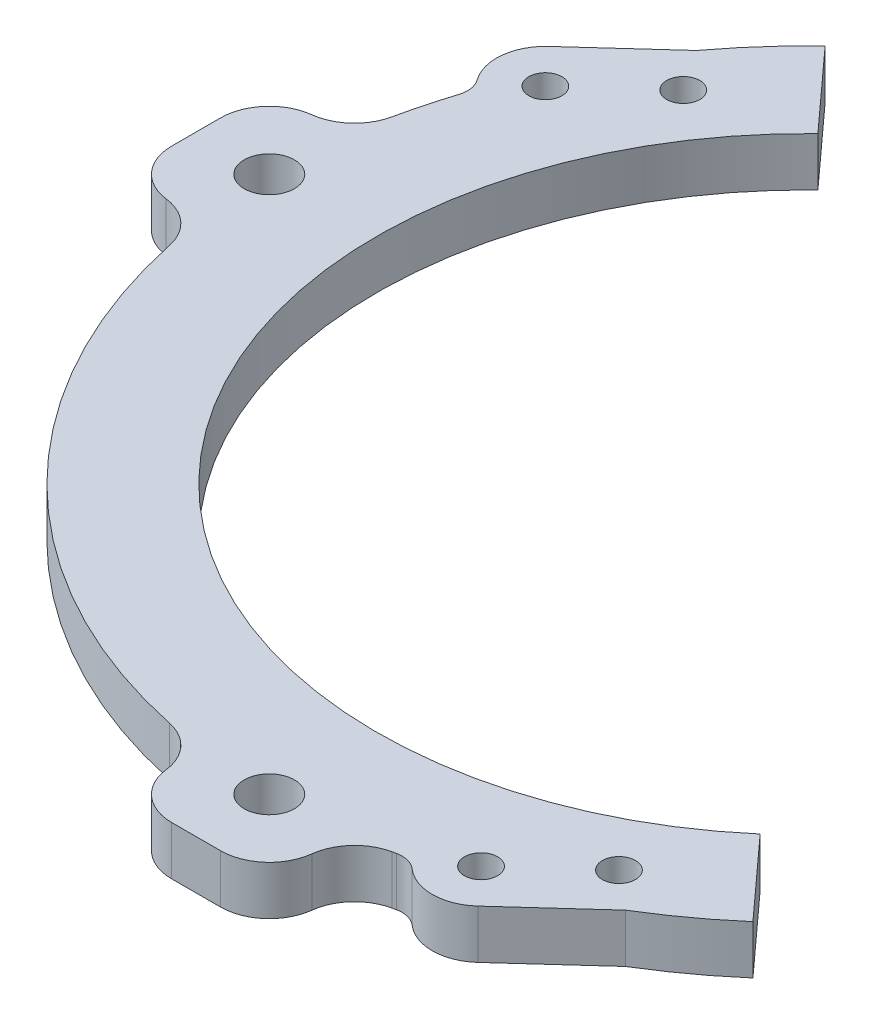
SolidWorks part; units mm, degrees
material "6061-T6 (SS)"
ref_plane "Front Plane" through (0, 0, 0) normal (0, 0, 1) x (1, 0, 0)
ref_plane "Top Plane" through (0, 0, 0) normal (0, 1, 0) x (1, 0, 0)
ref_plane "Right Plane" through (0, 0, 0) normal (1, 0, 0) x (0, 0, -1)
sketch "Sketch1" plane through (0, 0, 0) normal (0, 1, 0) x (1, 0, 0)
  circle A0 centre (0, 0) radius 55.88
  circle A1 centre (0, 0) radius 69.85
  dimension "D1" = 111.76
  dimension "D2" = 139.7
extrude "Boss-Extrude1" add sketch "Sketch1" along normal blind 6.35
sketch "Sketch5" plane through (0, 6.35, 0) normal (0, 1, 0) x (1, 0, 0)
  line L0 (0, 0) -> (0, 63.5) construction
  line L1 (-9.525, 63.5) -> (9.525, 63.5)
  line L2 (-9.525, 63.5) -> (-9.525, 73.025)
  line L3 (-3.175, 79.375) -> (3.175, 79.375)
  line L4 (9.525, 63.5) -> (9.525, 73.025)
  arc A0 (-9.525, 73.025) -> (-3.175, 79.375) centre (-3.175, 73.025) cw
  arc A1 (3.175, 79.375) -> (9.525, 73.025) centre (3.175, 73.025) cw
  point P10 (-9.525, 79.375)
  point P13 (9.525, 79.375)
  dimension "D4" = 6.35
  dimension "D1" = 63.5
  dimension "D2" = 79.375
  dimension "D3" = 19.05
extrude "Boss-Extrude2" add sketch "Sketch5" against normal blind 6.35
fillet "Fillet1" radius 6.35 2 edges at (9.525, 3.175, -69.1975) (-9.525, 3.175, -69.1975)
pattern_circular "CirPattern2" count 4 over 360 about axis through (0, 0, 0) along (0, 1, 0) of "Boss-Extrude2", "Fillet1"
hole_wizard "F (0.257) Diameter Hole1" positions "Sketch2" profile "Sketch3" hole size "F" standard "ANSI Inch" end condition through all
sketch "Sketch2" plane through (0, 6.35, 0) normal (0, 1, 0) x (1, 0, 0)
  point P0 (69.85, 0)
  dimension "D1" = 69.85
sketch "Sketch3" plane through (69.85, 6.35, 0) normal (1, 0, 0) x (0, 0, 1)
  line L0 (0, 0) -> (0, 6.35)
  line L1 (0, 6.35) -> (3.2639, 6.35)
  line L2 (3.2639, 6.35) -> (3.2639, 0)
  line L5 (3.2639, 0) -> (0, 0)
  line L11 (0, -6.35) -> (0, 107.95) construction
  dimension "Thru Hole Dia." = 6.5278
  dimension "Thru Hole Depth" = 6.35
pattern_circular "CirPattern1" count 4 over 360 about axis through (0, 0, 0) along (0, 1, 0) of "F (0.257) Diameter Hole1"
sketch "Sketch6" plane through (0, 0, 0) normal (0, -1, 0) x (1, 0, 0)
  line L0 (-57.4966, -60.8844) -> (55.1474, 63.0202)
  line L1 (-57.4966, -60.8844) -> (-55.1474, -63.0202)
  line L2 (55.1474, 63.0202) -> (57.4966, 60.8844)
  line L3 (-55.1474, -63.0202) -> (57.4966, 60.8844)
  line L4 (-57.4966, -60.8844) -> (57.4966, 60.8844) construction
  line L5 (55.1474, 63.0202) -> (-55.1474, -63.0202) construction
  point P1 (0, 0)
  dimension "D1" = 3.175
extrude "Cut-Extrude1" cut sketch "Sketch6" against normal through all contours L1 L3 L2 L0
sketch "Sketch8" plane through (0, 0, 0) normal (0, -1, 0) x (-1, 0, 0)
  line L0 (47.2922, 49.6598) -> (38.7491, 40.2627)
  line L1 (47.2922, 49.6598) -> (66.0864, 32.5736)
  line L2 (38.7491, 40.2627) -> (62.2418, 18.905)
  line L3 (66.5134, 23.6035) -> (62.2418, 18.905)
  line L4 (-36.3998, -42.3985) -> (-44.9429, -51.7956)
  line L5 (-36.3998, -42.3985) -> (-12.907, -63.7562)
  line L6 (-44.9429, -51.7956) -> (-26.1487, -68.8818)
  line L7 (-12.907, -63.7562) -> (-17.1786, -68.4547)
  line L8 (-36.3998, -42.3985) -> (-45.8002, -52.7386) construction
  arc A0 (-26.1487, -68.8818) -> (-17.1786, -68.4547) centre (-21.8771, -64.1832) ccw
  arc A1 (66.0864, 32.5736) -> (66.5134, 23.6035) centre (61.8148, 27.8751) cw
  point P16 (70.7849, 28.3021)
  dimension "D3" = 6.35
  dimension "D1" = 31.75
  dimension "D2" = 12.7
extrude "Boss-Extrude4" add sketch "Sketch8" against normal up to surface (6.35 mm away) up to face at (0, 6.35, 73.1139)
fillet "Fillet3" radius 3.175 2 edges at (-65.9575, 3.175, -22.992) (16.6227, 3.175, 67.8433)
hole_wizard "#18 (0.1695) Diameter Hole1" positions "Sketch9" profile "Sketch10" hole size "#18" standard "ANSI Inch" end condition through all
sketch "Sketch9" plane through (0, 0, 0) normal (0, -1, 0) x (-1, 0, 0)
  line L1 (61.8148, 27.8751) -> (52.4177, 36.4182) construction
  line L3 (66.0864, 32.5736) -> (56.0143, 41.7303) construction
  line L5 (48.1495, 50.6029) -> (38.7491, 40.2627) construction
  point P0 (61.8148, 27.8751)
  point P2 (52.4177, 36.4182)
  dimension "D1" = 12.7
  dimension "D2" = 12.7
  dimension "D3" = 6.35
sketch "Sketch10" plane through (-61.8148, 0, -27.8751) normal (1, 0, 0) x (0, 0, -1)
  line L0 (0, 0) -> (0, 6.35)
  line L1 (0, 6.35) -> (2.1526, 6.35)
  line L2 (2.1526, 6.35) -> (2.1526, 0)
  line L5 (2.1526, 0) -> (0, 0)
  line L11 (0, -6.35) -> (0, 107.95) construction
  dimension "Thru Hole Dia." = 4.3053
  dimension "Thru Hole Depth" = 6.35
ref_plane "Plane2" through (0, 0, 0) normal (-0.6727, 0, -0.7399) x (-0.7399, 0, 0.6727)
mirror "Mirror8" about plane through (0, 0, 0) normal (-0.6727, 0, -0.7399) of "#18 (0.1695) Diameter Hole1"
